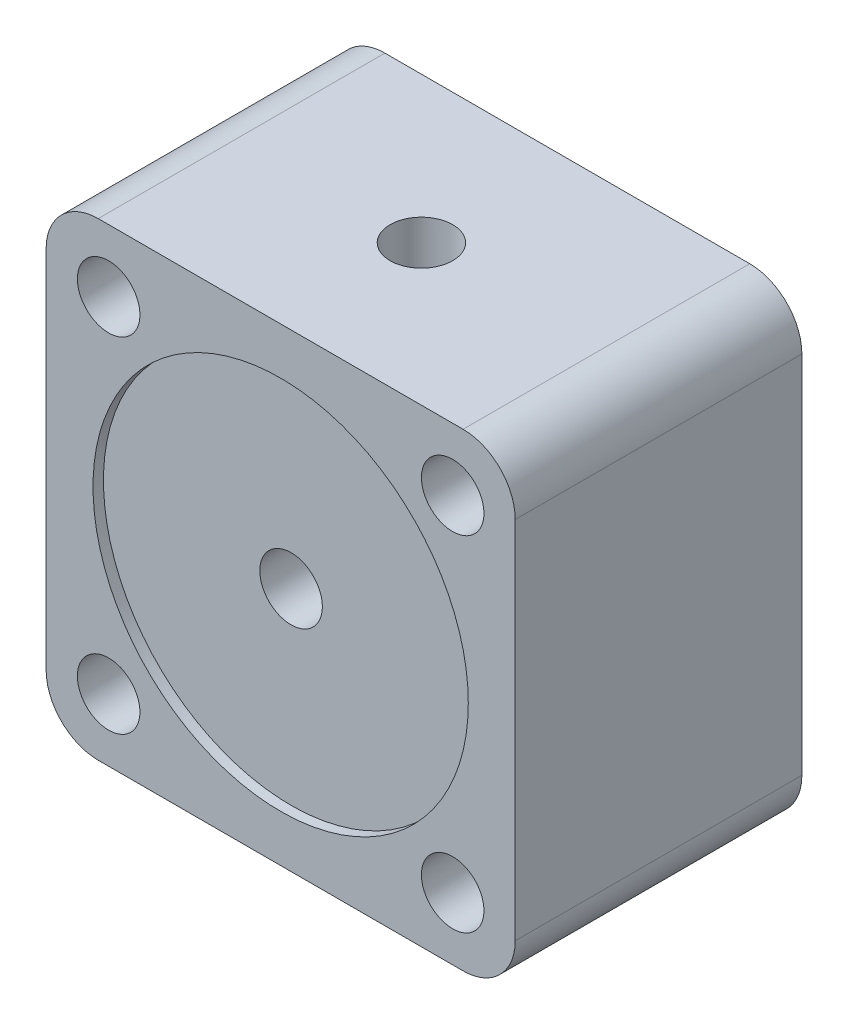
SolidWorks part; units mm, degrees
ref_plane "Front Plane" through (0, 0, 0) normal (0, 0, 1) x (1, 0, 0)
ref_plane "Top Plane" through (0, 0, 0) normal (0, 1, 0) x (1, 0, 0)
ref_plane "Right Plane" through (0, 0, 0) normal (1, 0, 0) x (0, 0, -1)
sketch "Sketch1" plane through (0, 0, 0) normal (0, 0, 1) x (1, 0, 0)
  line L0 (0, 40) -> (0, 5)
  line L1 (-5, 45) -> (-40, 45)
  line L2 (-45, 40) -> (-45, 5)
  line L3 (-40, 0) -> (-5, 0)
  line L4 (-22.5, 45) -> (-22.5, 0) construction
  line L5 (-22.6918, 22.5) -> (-22.5, 22.5) construction
  line L6 (-45, 0) -> (0, 45) construction
  line L7 (-22.6918, 22.5) -> (-22.5, 22.3066) construction
  line L8 (-45, 22.5) -> (0, 22.5) construction
  line L9 (-45, 45) -> (0, 0) construction
  circle A0 centre (-6, 39) radius 3
  circle A1 centre (-6, 6) radius 3
  circle A2 centre (-39, 6) radius 3
  circle A3 centre (-39, 39) radius 3
  arc A4 (-40, 45) -> (-45, 40) centre (-40, 40) ccw
  arc A5 (0, 40) -> (-5, 45) centre (-5, 40) ccw
  arc A6 (-45, 5) -> (-40, 0) centre (-40, 5) ccw
  arc A7 (-5, 0) -> (0, 5) centre (-5, 5) ccw
  dimension "D5" = 6
  dimension "D8" = 5
  dimension "D9" = 5
  dimension "D2" = 45
  dimension "D3" = 45
  dimension "D6" = 33
  dimension "D10" = 33
extrude "Boss-Extrude1" add sketch "Sketch1" along normal blind 27.5
sketch "Sketch3" plane through (0, 0, 27.5) normal (0, 0, 1) x (1, 0, 0)
  line L0 (-43.5355, 1.4645) -> (-1.4645, 43.5355) construction
  line L1 (-43.5355, 43.5355) -> (-1.4645, 1.4645) construction
  arc A0 (-45, 5) -> (-40, 0) centre (-40, 5) ccw construction
  arc A1 (0, 40) -> (-5, 45) centre (-5, 40) ccw construction
  arc A2 (-40, 45) -> (-45, 40) centre (-40, 40) ccw construction
  arc A3 (-5, 0) -> (0, 5) centre (-5, 5) ccw construction
  circle A4 centre (-22.5, 22.5) radius 18
  dimension "D1" = 36
extrude "Cut-Extrude1" cut sketch "Sketch3" against normal blind 1
sketch "Sketch7" plane through (0, 45, 0) normal (0, 1, 0) x (1, 0, 0)
  line L0 (-45, -27.5) -> (-45, 0) construction
  line L1 (-5, 0) -> (-40, 0) construction
  circle A0 centre (-22.5, -14) radius 3
  dimension "D1" = 22.5
  dimension "D3" = 6
  dimension "D2" = 14
extrude "Cut-Extrude2" cut sketch "Sketch7" against normal blind 20
sketch "Sketch8" plane through (0, 0, 26.5) normal (0, 0, 1) x (1, 0, 0)
  line L0 (-45, 40) -> (-45, 5) construction
  line L1 (-5, 45) -> (-40, 45) construction
  circle A0 centre (-22.5, 22.5) radius 3
  dimension "D1" = 22.5
  dimension "D3" = 6
  dimension "D2" = 22.5
extrude "Cut-Extrude3" cut sketch "Sketch8" against normal blind 16
